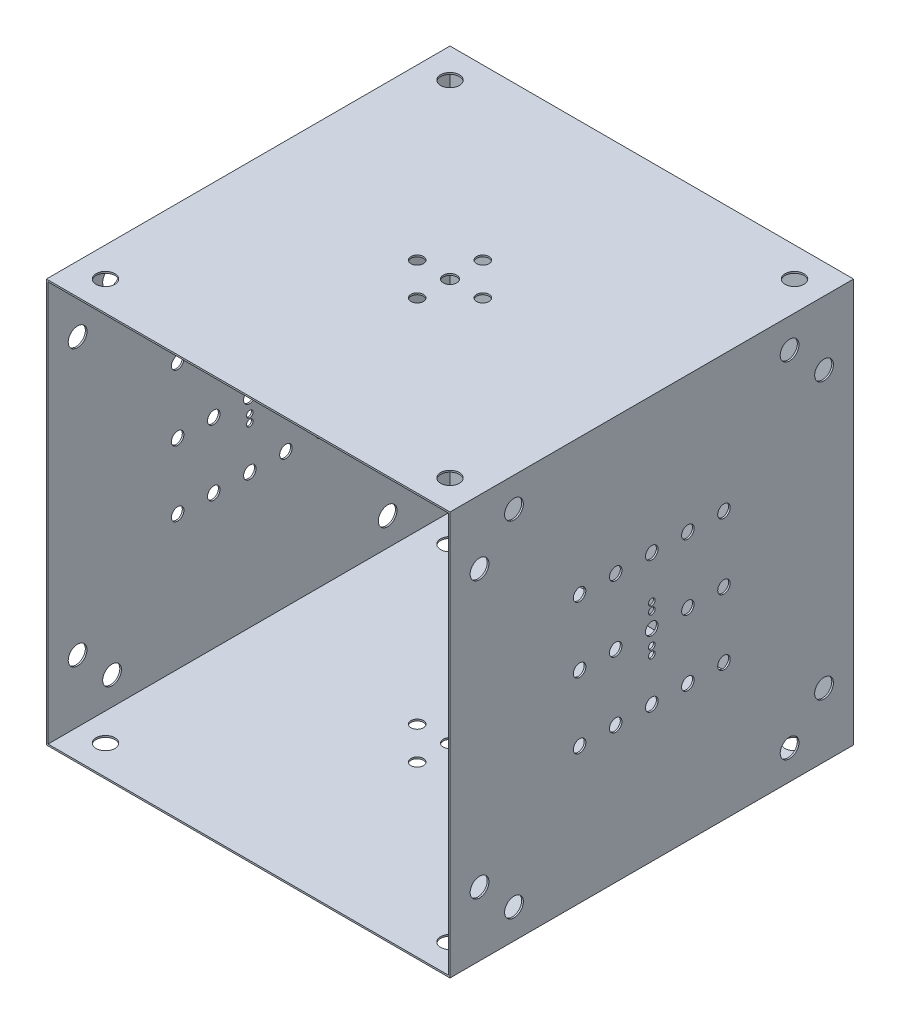
SolidWorks part; units mm, degrees
ref_plane "Front" through (0, 0, 0) normal (0, 0, 1) x (1, 0, 0)
ref_plane "Top" through (0, 0, 0) normal (0, 1, 0) x (1, 0, 0)
ref_plane "Right" through (0, 0, 0) normal (1, 0, 0) x (0, 0, -1)
sketch "Sketch1" plane through (0, 0, 0) normal (0, 0, 1) x (1, 0, 0)
  line L1 (-1230, 1230) -> (1230, 1230)
  line L2 (-1230, 1230) -> (-1230, -1230)
  line L3 (-1230, -1230) -> (1230, -1230)
  line L4 (1230, 1230) -> (1230, -1230)
  line L5 (-1230, 1230) -> (1230, -1230) construction
  line L6 (-1230, -1230) -> (1230, 1230) construction
  point P0 (0, 0)
  dimension "D1" = 2460
  dimension "D2" = 2460
extrude "Boss-Extrude1" add sketch "Sketch1" along normal blind 2460
shell "Shell1" thickness 10
sketch "Sketch2" plane through (-1230, 0, 0) normal (-1, 0, 0) x (0, 0, 1)
  line L0 (0, 0) -> (2460, 0) construction
  line L1 (0, 1230) -> (0, -1230) construction
  line L2 (2460, 1230) -> (2460, -1230) construction
  line L3 (1230, 1230) -> (1230, -1230) construction
  line L4 (2460, 1230) -> (0, 1230) construction
  line L5 (2460, -1230) -> (0, -1230) construction
  line L6 (1230, 0) -> (0, 1230) construction
  line L7 (1230, 0) -> (1010, 0) construction
  line L8 (790, 0) -> (790, 400) construction
  circle A0 centre (1230, 0) radius 38.1
  circle A1 centre (1010, 0) radius 38.1
  circle A2 centre (790, 0) radius 38.1
  circle A3 centre (1450, 0) radius 38.1
  circle A4 centre (1670, 0) radius 38.1
  circle A5 centre (790, 400) radius 38.1
  circle A6 centre (1010, 400) radius 38.1
  circle A7 centre (1230, 400) radius 38.1
  circle A8 centre (1450, 400) radius 38.1
  circle A9 centre (1670, 400) radius 38.1
  circle A10 centre (1670, -400) radius 38.1
  circle A11 centre (1450, -400) radius 38.1
  circle A12 centre (1230, -400) radius 38.1
  circle A13 centre (1010, -400) radius 38.1
  circle A14 centre (790, -400) radius 38.1
  circle A15 centre (1230, 92.5) radius 20
  circle A16 centre (1230, 140) radius 20
  circle A17 centre (1230, -140) radius 20
  circle A18 centre (1230, -92.5) radius 20
  circle A19 centre (390, 1050) radius 57.15
  circle A20 centre (180, 840) radius 57.15
  circle A21 centre (2280, 840) radius 57.15
  circle A22 centre (2070, 1050) radius 57.15
  circle A23 centre (2280, -840) radius 57.15
  circle A24 centre (2070, -1050) radius 57.15
  circle A25 centre (180, -840) radius 57.15
  circle A26 centre (390, -1050) radius 57.15
  dimension "D1" = 76.2
  dimension "D6" = 40
  dimension "D8" = 0
  dimension "D10" = 40
  dimension "D11" = 114.3
  dimension "D3" = 220
  dimension "D5" = 400
  dimension "D7" = 92.5
  dimension "D9" = 140
  dimension "D12" = 1050
  dimension "D13" = 840
  dimension "D2" = 3
  dimension "D4" = 2
extrude "Cut-Extrude1" cut sketch "Sketch2" against normal through all
sketch "Sketch3" plane through (0, 1230, 0) normal (0, 1, 0) x (1, 0, 0)
  line L0 (-1230, -1230) -> (1230, -1230) construction
  line L1 (-1230, -2460) -> (-1230, 0) construction
  line L2 (1230, -2460) -> (1230, 0) construction
  line L3 (0, 0) -> (0, -2460) construction
  line L4 (1230, -2460) -> (-1230, -2460) construction
  line L5 (-1230, 0) -> (0, -1230) construction
  circle A0 centre (0, -1230) radius 41.2
  circle A1 centre (-200, -1230) radius 38.1
  circle A2 centre (200, -1230) radius 38.1
  circle A3 centre (0, -1430) radius 38.1
  circle A4 centre (0, -1030) radius 38.1
  circle A5 centre (-1050, -180) radius 57.15
  circle A6 centre (1050, -180) radius 57.15
  circle A7 centre (1050, -2280) radius 57.15
  circle A8 centre (-1050, -2280) radius 57.15
  dimension "D1" = 82.4
  dimension "D2" = 76.2
  dimension "D4" = 114.3
  dimension "D3" = 200
  dimension "D5" = 1050
extrude "Cut-Extrude2" cut sketch "Sketch3" against normal through all
sketch "Sketch4" plane through (0, 0, 0) normal (0, 0, -1) x (-1, 0, 0)
  line L0 (-1230, 0) -> (1230, 0) construction
  line L1 (-1230, -1230) -> (-1230, 1230) construction
  line L2 (1230, 1230) -> (1230, -1230) construction
  line L3 (0, 1230) -> (0, -1230) construction
  line L4 (-1230, 1230) -> (1230, 1230) construction
  line L5 (1230, -1230) -> (-1230, -1230) construction
  line L6 (0, 0) -> (-1230, 1230) construction
  circle A0 centre (0, 0) radius 82.55
  circle A1 centre (-222, 382) radius 82.55
  circle A2 centre (222, -382) radius 82.55
  circle A3 centre (-900, 900) radius 57.15
  circle A4 centre (900, 900) radius 57.15
  circle A5 centre (900, -900) radius 57.15
  circle A6 centre (-900, -900) radius 57.15
  circle A7 centre (0, 140) radius 25
  circle A8 centre (0, -140) radius 25
  dimension "D1" = 165.1
  dimension "D4" = 165.1
  dimension "D7" = 165.1
  dimension "D8" = 114.3
  dimension "D10" = 50
  dimension "D2" = 382
  dimension "D3" = 222
  dimension "D5" = 382
  dimension "D6" = 222
  dimension "D9" = 900
  dimension "D11" = 140
extrude "Cut-Extrude3" cut sketch "Sketch4" against normal through all
